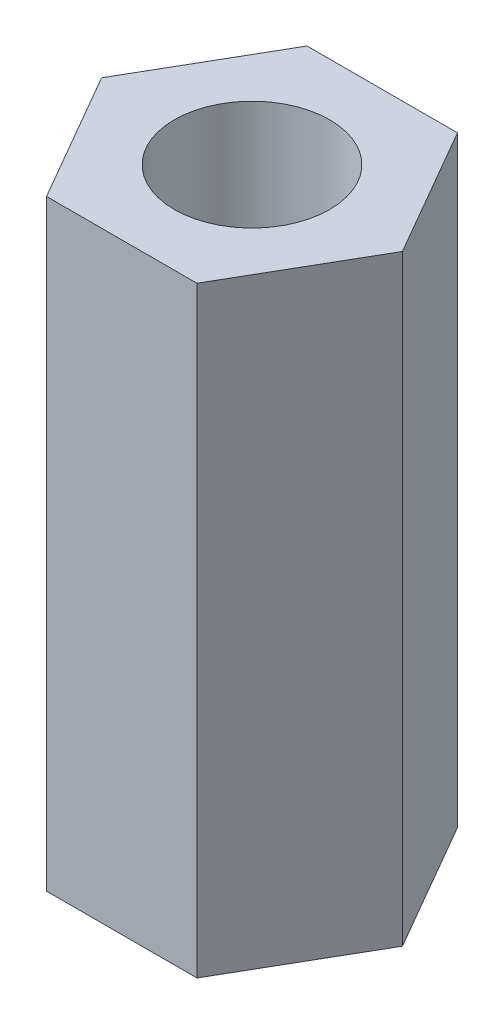
SolidWorks part; units mm, degrees
ref_plane "Front Plane" through (0, 0, 0) normal (0, 0, 1) x (1, 0, 0)
ref_plane "Top Plane" through (0, 0, 0) normal (0, 1, 0) x (1, 0, 0)
ref_plane "Right Plane" through (0, 0, 0) normal (1, 0, 0) x (0, 0, -1)
sketch "Sketch1" plane through (0, 0, 0) normal (0, 1, 0) x (1, 0, 0)
  line L1 (2.5, 0) -> (1.25, 2.1651)
  line L2 (1.25, 2.1651) -> (-1.25, 2.1651)
  line L3 (-1.25, 2.1651) -> (-2.5, 0)
  line L4 (-2.5, 0) -> (-1.25, -2.1651)
  line L5 (-1.25, -2.1651) -> (1.25, -2.1651)
  line L6 (1.25, -2.1651) -> (2.5, 0)
  circle A0 centre (0, 0) radius 2.1651 construction
  dimension "D1" = 2.5
extrude "Boss-Extrude1" add sketch "Sketch1" along normal blind 10
sketch "Sketch2" plane through (0, 10, 0) normal (0, 1, 0) x (1, 0, 0)
  circle A0 centre (0, 0) radius 1.2919
extrude "Cut-Extrude1" cut sketch "Sketch2" against normal through all
